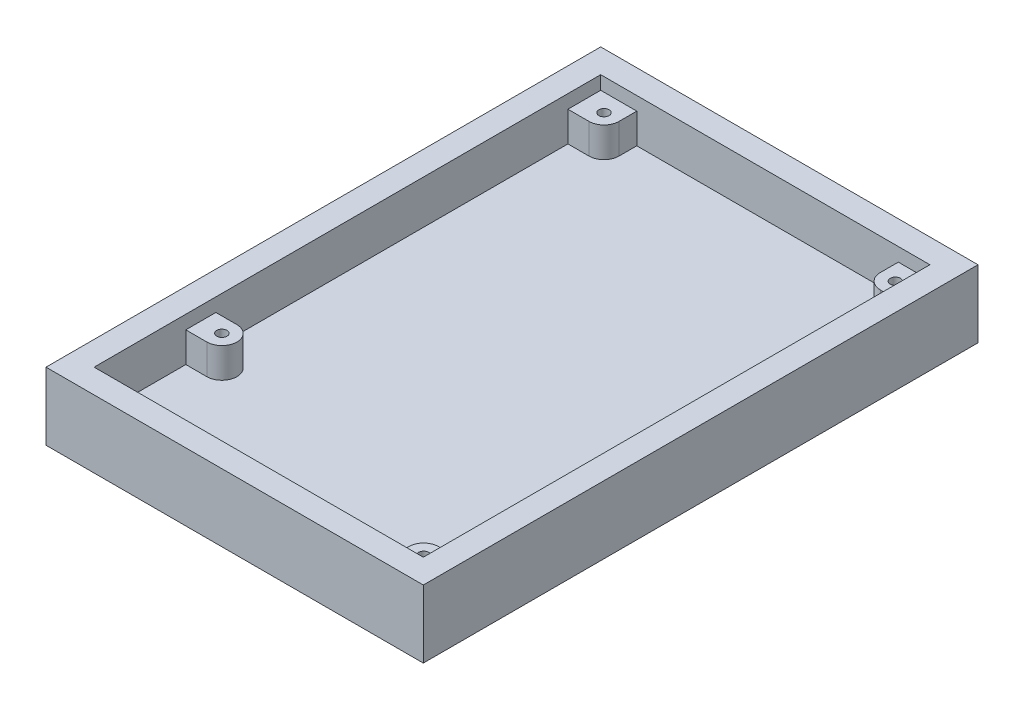
SolidWorks part; units mm, degrees
ref_plane "Front Plane" through (0, 0, 0) normal (0, 0, 1) x (1, 0, 0)
ref_plane "Top Plane" through (0, 0, 0) normal (0, 1, 0) x (1, 0, 0)
ref_plane "Right Plane" through (0, 0, 0) normal (1, 0, 0) x (0, 0, -1)
sketch "Sketch1" plane through (0, 0, 0) normal (0, 1, 0) x (1, 0, 0)
  line L1 (-27.375, -42.125) -> (27.375, -42.125) construction
  line L2 (-27.375, -42.125) -> (-27.375, 42.125) construction
  line L3 (-27.375, 42.125) -> (27.375, 42.125) construction
  line L4 (27.375, -42.125) -> (27.375, 42.125) construction
  line L5 (-27.375, -42.125) -> (27.375, 42.125) construction
  line L6 (-27.375, 42.125) -> (27.375, -42.125) construction
  line L7 (-31.375, -46.125) -> (31.375, -46.125)
  line L8 (-31.375, -46.125) -> (-31.375, 46.125)
  line L9 (-31.375, 46.125) -> (31.375, 46.125)
  line L10 (31.375, -46.125) -> (31.375, 46.125)
  line L11 (-31.375, -46.125) -> (31.375, 46.125) construction
  line L12 (-31.375, 46.125) -> (31.375, -46.125) construction
  point P0 (0, 0)
  point P6 (0, 0)
  dimension "D1" = 84.25
  dimension "D2" = 54.75
  dimension "D3" = 4
  dimension "D4" = 4
extrude "Boss-Extrude1" add sketch "Sketch1" along normal blind 4
sketch "Sketch2" plane through (0, 4, 0) normal (0, 1, 0) x (1, 0, 0)
  line L0 (-27.375, -42.125) -> (27.375, -42.125)
  line L1 (-27.375, -42.125) -> (-27.375, 42.125)
  line L2 (-27.375, 42.125) -> (27.375, 42.125)
  line L3 (27.375, -42.125) -> (27.375, 42.125)
  line L4 (-27.375, -42.125) -> (27.375, 42.125) construction
  line L5 (-27.375, 42.125) -> (27.375, -42.125) construction
  line L6 (-31.375, -46.125) -> (31.375, -46.125)
  line L7 (-31.375, -46.125) -> (-31.375, 46.125)
  line L8 (-31.375, 46.125) -> (31.375, 46.125)
  line L9 (31.375, -46.125) -> (31.375, 46.125)
  line L10 (-31.375, -46.125) -> (31.375, 46.125) construction
  line L11 (-31.375, 46.125) -> (31.375, -46.125) construction
  line L12 (0, 0) -> (-0.906, 0) construction
  point P0 (0, 0)
  point P5 (0, 0)
  point P10 (0, 0)
  dimension "D1" = 84.25
  dimension "D2" = 54.75
  dimension "D3" = 4
  dimension "D4" = 4
extrude "Boss-Extrude2" add sketch "Sketch2" along normal blind 7.25
sketch "Sketch3" plane through (0, 4, 0) normal (0, 1, 0) x (1, 0, 0)
  line L0 (0, 42.125) -> (0, 40.0348) construction
  line L1 (27.375, 42.125) -> (-27.375, 42.125) construction
  line L2 (27.375, 0) -> (25.3413, 0) construction
  line L3 (27.375, -42.125) -> (27.375, 42.125) construction
  line L4 (-23.875, 39.175) -> (-23.875, 42.125) construction
  line L5 (-23.875, 39.175) -> (-27.375, 39.175) construction
  line L6 (-27.375, 42.125) -> (-27.375, -42.125) construction
  line L7 (27.375, 39.125) -> (24.625, 39.125) construction
  line L8 (24.625, 39.125) -> (24.625, 42.125) construction
  line L9 (27.375, -39.575) -> (24.875, -39.575) construction
  line L10 (24.875, -39.575) -> (24.875, -42.125) construction
  line L11 (-27.375, -42.125) -> (27.375, -42.125) construction
  line L12 (-27.375, -24.375) -> (-23.875, -24.375) construction
  line L13 (-23.875, -24.375) -> (-23.875, -42.125) construction
  line L14 (-21.375, 39.175) -> (-21.375, 42.125)
  line L15 (-21.375, 42.125) -> (-27.375, 42.125)
  line L16 (-27.375, 42.125) -> (-27.375, 36.675)
  line L17 (-27.375, 36.675) -> (-23.875, 36.675)
  line L18 (22.125, 39.125) -> (22.125, 42.125)
  line L19 (22.125, 42.125) -> (27.375, 42.125)
  line L20 (27.375, 42.125) -> (27.375, 36.625)
  line L21 (27.375, 36.625) -> (24.625, 36.625)
  line L22 (22.375, -39.575) -> (22.375, -42.125)
  line L23 (22.375, -42.125) -> (27.375, -42.125)
  line L25 (27.375, -42.125) -> (27.375, -37.075)
  line L26 (27.375, -37.075) -> (24.875, -37.075)
  line L27 (-23.875, -26.875) -> (-27.375, -26.875)
  line L28 (-27.375, -26.875) -> (-27.375, -21.875)
  line L29 (-27.375, -21.875) -> (-23.875, -21.875)
  circle A0 centre (-23.875, 39.175) radius 0.85
  circle A1 centre (24.625, 39.125) radius 0.85
  circle A2 centre (24.875, -39.575) radius 0.85
  circle A3 centre (-23.875, -24.375) radius 0.85
  arc A4 (-23.875, 36.675) -> (-21.375, 39.175) centre (-23.875, 39.175) ccw
  arc A5 (22.125, 39.125) -> (24.625, 36.625) centre (24.625, 39.125) ccw
  arc A6 (24.875, -37.075) -> (22.375, -39.575) centre (24.875, -39.575) ccw
  arc A7 (-23.875, -26.875) -> (-23.875, -21.875) centre (-23.875, -24.375) ccw
  dimension "D3" = 1.7
  dimension "D10" = 5
  dimension "D1" = 3.5
  dimension "D2" = 2.95
  dimension "D4" = 2.75
  dimension "D5" = 3
  dimension "D6" = 2.55
  dimension "D8" = 3.5
  dimension "D9" = 17.75
extrude "Boss-Extrude3" add sketch "Sketch3" along normal blind 5
